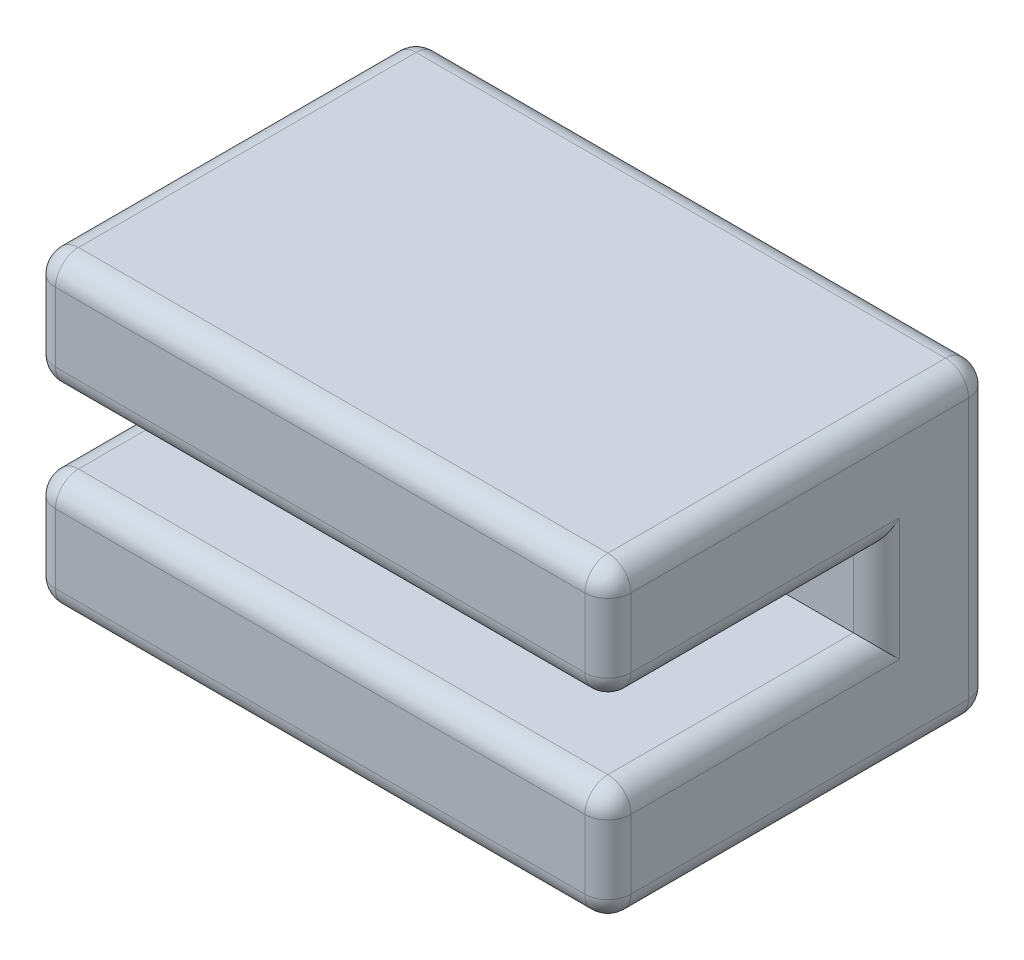
SolidWorks part; units mm, degrees
ref_plane "Front Plane" through (0, 0, 0) normal (0, 0, 1) x (1, 0, 0)
ref_plane "Top Plane" through (0, 0, 0) normal (0, 1, 0) x (1, 0, 0)
ref_plane "Right Plane" through (0, 0, 0) normal (1, 0, 0) x (0, 0, -1)
sketch "Sketch1" plane through (0, 0, 0) normal (0, 0, 1) x (1, 0, 0)
  line L1 (0, 0) -> (-15, 0)
  line L2 (0, 0) -> (0, 8)
  line L3 (0, 8) -> (-15, 8)
  line L4 (-15, 0) -> (-15, 8)
  dimension "D1" = 8
  dimension "D2" = 15
extrude "Boss-Extrude1" add sketch "Sketch1" along normal blind 10
sketch "Sketch2" plane through (0, 0, 10) normal (0, 0, 1) x (1, 0, 0)
  line L0 (-15, 8) -> (-15, 0) construction
  line L1 (-15, 3) -> (0, 3)
  line L2 (-15, 3) -> (-15, 5)
  line L3 (-15, 5) -> (0, 5)
  line L4 (0, 3) -> (0, 5)
  line L5 (0, 0) -> (0, 8) construction
  line L6 (-15, 0) -> (0, 0) construction
  dimension "D1" = 2
  dimension "D2" = 3
extrude "Cut-Extrude1" cut sketch "Sketch2" against normal blind 7
fillet "Fillet1" radius 0.6 22 edges at (0, 8, 5) (0, 3, 6.5) (0, 4, 3) (0, 5, 6.5) (-7.5, 8, 10) (0, 6.5, 10) (-7.5, 5, 10) (0, 1.5, 10) (-7.5, 3, 10) (-7.5, 0, 10) (0, 0, 5) (-15, 3, 6.5) (-15, 1.5, 10) (-15, 0, 5) (-15, 8, 5) (-15, 6.5, 10) (-15, 5, 6.5) (-15, 4, 3) (-7.5, 8, 0) (-15, 4, 0) (-7.5, 0, 0) (0, 4, 0)
